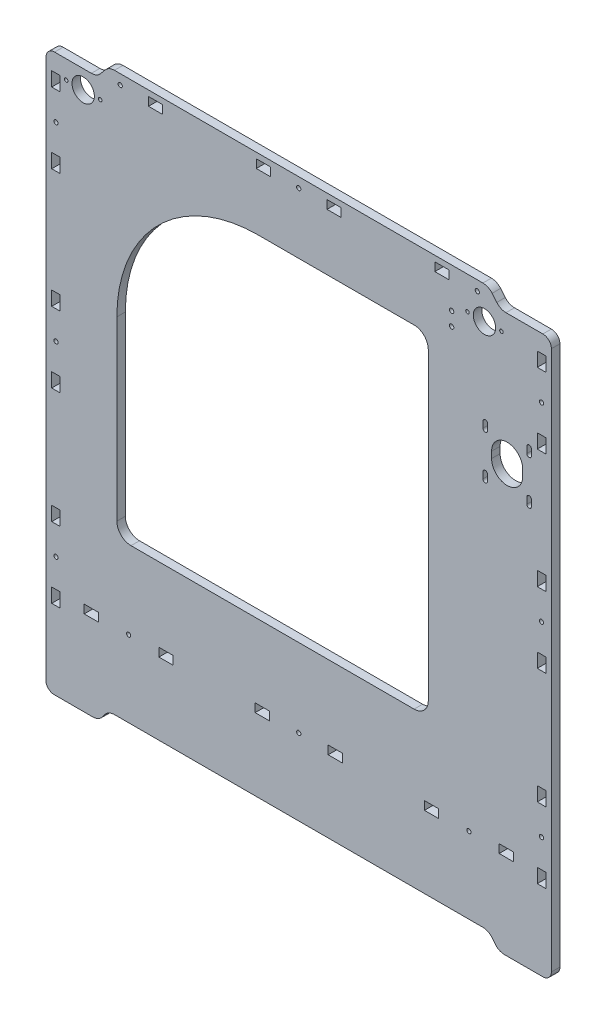
SolidWorks part; units mm, degrees
ref_plane "Спереди" through (0, 0, 0) normal (0, 0, 1) x (1, 0, 0)
ref_plane "Сверху" through (0, 0, 0) normal (0, 1, 0) x (1, 0, 0)
ref_plane "Справа" through (0, 0, 0) normal (1, 0, 0) x (0, 0, -1)
sketch "Эскиз1" plane through (0, 0, 0) normal (0, 0, 1) x (1, 0, 0)
  line L0 (133.6555, 83.4698) -> (133.6555, 87.9698)
  line L1 (133.6555, 118.9698) -> (133.6555, 114.4698)
  line L2 (130.4555, 83.4698) -> (130.4555, 87.9698)
  line L3 (158.5555, 98.9698) -> (158.5555, 103.4698)
  line L4 (130.4555, 118.9698) -> (130.4555, 114.4698)
  line L5 (161.4555, 118.9698) -> (161.4555, 114.4698)
  line L6 (164.6555, 118.9698) -> (164.6555, 114.4698)
  line L7 (136.5555, 98.9698) -> (136.5555, 103.4698)
  line L8 (161.4555, 83.4698) -> (161.4555, 87.9698)
  line L9 (164.6555, 83.4698) -> (164.6555, 87.9698)
  line L10 (-174.1809, 36.7423) -> (-174.1809, 46.7423)
  line L11 (99.1091, -139.9977) -> (89.1091, -139.9977)
  line L12 (89.1091, -139.9977) -> (89.1091, -133.9977)
  line L13 (89.1091, -133.9977) -> (99.1091, -133.9977)
  line L14 (99.1091, -133.9977) -> (99.1091, -139.9977)
  line L15 (151.9091, -139.9977) -> (141.9091, -139.9977)
  line L16 (141.9091, -139.9977) -> (141.9091, -133.9977)
  line L17 (141.9091, -133.9977) -> (151.9091, -133.9977)
  line L18 (151.9091, -133.9977) -> (151.9091, -139.9977)
  line L19 (-19.6709, 193.3023) -> (-29.6709, 193.3023)
  line L20 (-29.6709, 193.3023) -> (-29.6709, 199.3023)
  line L21 (-29.6709, 199.3023) -> (-19.6709, 199.3023)
  line L22 (-19.6709, 199.3023) -> (-19.6709, 193.3023)
  line L23 (30.3091, 193.3023) -> (20.3091, 193.3023)
  line L24 (20.3091, 193.3023) -> (20.3091, 199.3023)
  line L25 (20.3091, 199.3023) -> (30.3091, 199.3023)
  line L26 (30.3091, 199.3023) -> (30.3091, 193.3023)
  line L27 (-141.2709, -139.9977) -> (-151.2709, -139.9977)
  line L28 (-151.2709, -139.9977) -> (-151.2709, -133.9977)
  line L29 (-151.2709, -133.9977) -> (-141.2709, -133.9977)
  line L30 (-141.2709, -133.9977) -> (-141.2709, -139.9977)
  line L31 (-88.4709, -139.9977) -> (-98.4709, -139.9977)
  line L32 (-98.4709, -139.9977) -> (-98.4709, -133.9977)
  line L33 (-98.4709, -133.9977) -> (-88.4709, -133.9977)
  line L34 (-88.4709, -133.9977) -> (-88.4709, -139.9977)
  line L35 (-20.4709, -139.9977) -> (-30.4709, -139.9977)
  line L36 (-30.4709, -139.9977) -> (-30.4709, -133.9977)
  line L37 (-30.4709, -133.9977) -> (-20.4709, -133.9977)
  line L38 (-20.4709, -133.9977) -> (-20.4709, -139.9977)
  line L39 (31.1091, -139.9977) -> (21.1091, -139.9977)
  line L40 (21.1091, -139.9977) -> (21.1091, -133.9977)
  line L41 (21.1091, -133.9977) -> (31.1091, -133.9977)
  line L42 (31.1091, -133.9977) -> (31.1091, -139.9977)
  line L43 (-174.1809, 46.7423) -> (-168.1809, 46.7423)
  line L44 (-168.1809, 46.7423) -> (-168.1809, 36.7423)
  line L45 (-168.1809, 36.7423) -> (-174.1809, 36.7423)
  line L46 (-174.1809, -13.2577) -> (-174.1809, -3.2577)
  line L47 (-174.1809, -3.2577) -> (-168.1809, -3.2577)
  line L48 (-168.1809, -3.2577) -> (-168.1809, -13.2577)
  line L49 (-168.1809, -13.2577) -> (-174.1809, -13.2577)
  line L50 (-174.1809, 170.9023) -> (-174.1809, 180.9023)
  line L51 (-174.1809, 180.9023) -> (-168.1809, 180.9023)
  line L52 (-168.1809, 180.9023) -> (-168.1809, 170.9023)
  line L53 (-168.1809, 170.9023) -> (-174.1809, 170.9023)
  line L54 (-174.1809, 120.9023) -> (-174.1809, 130.9023)
  line L55 (-174.1809, 130.9023) -> (-168.1809, 130.9023)
  line L56 (-168.1809, 130.9023) -> (-168.1809, 120.9023)
  line L57 (-168.1809, 120.9023) -> (-174.1809, 120.9023)
  line L58 (-174.1809, -94.9877) -> (-174.1809, -84.9877)
  line L59 (-174.1809, -84.9877) -> (-168.1809, -84.9877)
  line L62 (-174.1809, -144.9777) -> (-174.1809, -134.9777)
  line L63 (-174.1809, -134.9777) -> (-168.1809, -134.9777)
  line L64 (-168.1809, -134.9777) -> (-168.1809, -144.9777)
  line L65 (-168.1809, -144.9777) -> (-174.1809, -144.9777)
  line L66 (168.8191, 36.7421) -> (168.8191, 46.7421)
  line L67 (168.8191, 46.7421) -> (174.8191, 46.7421)
  line L68 (174.8191, 46.7421) -> (174.8191, 36.7421)
  line L69 (174.8191, 36.7421) -> (168.8191, 36.7421)
  line L70 (168.8191, -13.2579) -> (168.8191, -3.2579)
  line L71 (168.8191, -3.2579) -> (174.8191, -3.2579)
  line L72 (174.8191, -3.2579) -> (174.8191, -13.2579)
  line L73 (174.8191, -13.2579) -> (168.8191, -13.2579)
  line L74 (168.8191, -94.9879) -> (168.8191, -84.9879)
  line L75 (168.8191, -84.9879) -> (174.8191, -84.9879)
  line L76 (174.8191, -84.9879) -> (174.8191, -94.9879)
  line L77 (174.8191, -94.9879) -> (168.8191, -94.9879)
  line L78 (168.8191, -144.9779) -> (168.8191, -134.9779)
  line L79 (168.8191, -134.9779) -> (174.8191, -134.9779)
  line L80 (174.8191, -134.9779) -> (174.8191, -144.9779)
  line L81 (174.8191, -144.9779) -> (168.8191, -144.9779)
  line L82 (168.8191, 170.9021) -> (168.8191, 180.9021)
  line L83 (168.8191, 180.9021) -> (174.8191, 180.9021)
  line L84 (175.1452, 170.9021) -> (168.8191, 170.9021)
  line L85 (168.8191, 120.9021) -> (168.8191, 130.9021)
  line L86 (168.8191, 130.9021) -> (174.8191, 130.9021)
  line L87 (174.8191, 130.9021) -> (174.8191, 120.9021)
  line L88 (174.8191, 120.9021) -> (168.8191, 120.9021)
  line L89 (-105.8209, 199.3023) -> (-95.8209, 199.3023)
  line L90 (-95.8209, 199.3023) -> (-95.8209, 193.3023)
  line L91 (-95.8209, 193.3023) -> (-105.8209, 193.3023)
  line L92 (-105.8209, 193.3023) -> (-105.8209, 199.3023)
  line L94 (96.4591, 193.3023) -> (96.4591, 199.3023)
  line L96 (146.7286, 193.3021) -> (172.7648, 193.3021)
  line L97 (106.4591, 193.3023) -> (96.4591, 193.3023)
  line L99 (-136.3916, 200.266) -> (-139.6874, 196.3386)
  line L100 (130.4099, 203.3023) -> (-129.8802, 203.3023)
  line L101 (136.9212, 200.266) -> (140.2171, 196.3385)
  line L102 (174.8191, 170.9781) -> (175.1452, 170.9021)
  line L104 (96.4591, 199.3023) -> (106.4591, 199.3023)
  line L105 (174.8191, 180.9021) -> (174.8191, 170.9781)
  line L106 (139.2171, -196.9614) -> (136.9212, -193.9418)
  line L107 (-129.8802, -190.9055) -> (130.4099, -190.9055)
  line L108 (-172.2352, -199.9977) -> (-145.1988, -199.9977)
  line L109 (-138.6874, -196.9614) -> (-136.3916, -193.9418)
  line L110 (172.7648, -199.9977) -> (145.7284, -199.9977)
  line L111 (-178.1809, 187.3023) -> (-178.1809, -195.6332)
  line L112 (178.8191, 187.3133) -> (178.8191, -193.998)
  line L113 (-174.1809, -94.9877) -> (-168.1809, -94.9877)
  line L114 (-168.1809, -94.9877) -> (-168.1809, -84.9877)
  line L115 (-172.1809, 193.3023) -> (-146.1988, 193.3023)
  line L116 (106.4591, 199.3023) -> (106.4591, 193.3023)
  line L117 (-198.706, -139.9977) -> (230.9068, -139.9977) construction
  line L118 (-130.8326, 180.3023) -> (-166.8576, 180.3023) construction
  line L119 (113.3107, 180.3023) -> (155.186, 180.3023) construction
  line L121 (-276.4475, 153.3023) -> (140.2171, 153.3023) construction
  line L124 (-128.1809, -71.6977) -> (-128.1809, 53.3023)
  line L126 (-28.1809, 153.3023) -> (81.8191, 153.3023)
  line L127 (91.8191, 143.3023) -> (91.8191, -71.6977)
  line L128 (81.8191, -81.6977) -> (-118.1809, -81.6977)
  arc A0 (158.5555, 103.4698) -> (136.5555, 103.4698) centre (147.5555, 103.4698) ccw
  arc A1 (161.4555, 83.4698) -> (164.6555, 83.4698) centre (163.0555, 83.4698) ccw
  arc A2 (136.5555, 98.9698) -> (158.5555, 98.9698) centre (147.5555, 98.9698) ccw
  arc A3 (130.4555, 83.4698) -> (133.6555, 83.4698) centre (132.0555, 83.4698) ccw
  arc A4 (164.6555, 87.9698) -> (161.4555, 87.9698) centre (163.0555, 87.9698) ccw
  circle A5 centre (108.3191, 165.6023) radius 1.55
  circle A6 centre (108.3191, 175.3023) radius 1.55
  arc A7 (130.4555, 114.4698) -> (133.6555, 114.4698) centre (132.0555, 114.4698) ccw
  arc A8 (133.6555, 118.9698) -> (130.4555, 118.9698) centre (132.0555, 118.9698) ccw
  arc A9 (164.6555, 118.9698) -> (161.4555, 118.9698) centre (163.0555, 118.9698) ccw
  arc A10 (161.4555, 114.4698) -> (164.6555, 114.4698) centre (163.0555, 114.4698) ccw
  arc A11 (133.6555, 87.9698) -> (130.4555, 87.9698) centre (132.0555, 87.9698) ccw
  circle A12 centre (131.5191, 180.3023) radius 7.9
  circle A13 centre (-151.9809, 180.3023) radius 7.9
  arc A14 (-129.8802, 203.3023) -> (-136.3916, 200.266) centre (-129.8802, 194.8023) ccw
  arc A15 (-146.1988, 193.3023) -> (-139.6874, 196.3386) centre (-146.1988, 201.8023) ccw
  arc A17 (140.2171, 196.3385) -> (146.7286, 193.3021) centre (146.7286, 201.8021) ccw
  arc A18 (136.9212, 200.266) -> (130.4099, 203.3023) centre (130.4099, 194.8023) ccw
  arc A19 (178.8191, 187.3133) -> (172.7648, 193.3021) centre (172.8191, 187.3023) ccw
  arc A20 (136.9212, -193.9418) -> (130.4099, -190.9055) centre (130.4099, -199.4055) ccw
  arc A21 (-178.1809, -195.6332) -> (-172.2352, -199.9977) centre (-172.4074, -194.0002) ccw
  arc A22 (-145.1988, -199.9977) -> (-138.6874, -196.9614) centre (-145.1988, -191.4977) ccw
  arc A23 (139.2171, -196.9614) -> (145.7284, -199.9977) centre (145.7284, -191.4977) ccw
  arc A24 (-129.8802, -190.9055) -> (-136.3916, -193.9418) centre (-129.8802, -199.4055) ccw
  circle A25 centre (-171.1809, 150.9023) radius 1.5
  arc A26 (172.7648, -199.9977) -> (178.8191, -193.998) centre (172.8191, -193.998) ccw
  circle A27 centre (-171.1809, 16.7423) radius 1.5
  circle A28 centre (171.8191, 150.9021) radius 1.5
  circle A29 centre (126.4591, 196.3023) radius 1.5
  circle A30 centre (-125.8209, 196.3023) radius 1.5
  circle A31 centre (0.3191, 196.3023) radius 1.5
  circle A32 centre (-119.8709, -136.9977) radius 1.5
  circle A33 centre (-171.1809, -114.9677) radius 1.5
  circle A34 centre (0.3191, -136.9977) radius 1.5
  circle A35 centre (120.5091, -136.9977) radius 1.5
  circle A36 centre (171.8191, -114.9679) radius 1.5
  circle A37 centre (171.8191, 16.7421) radius 1.5
  arc A38 (-178.1809, 187.3023) -> (-172.1809, 193.3023) centre (-172.1809, 187.3023) cw
  circle A39 centre (-139.9809, 180.3023) radius 1.25
  circle A40 centre (-163.9809, 180.3023) radius 1.25
  circle A41 centre (119.5191, 180.3023) radius 1.25
  circle A42 centre (143.5191, 180.3023) radius 1.25
  arc A43 (81.8191, 153.3023) -> (91.8191, 143.3023) centre (81.8191, 143.3023) cw
  arc A44 (91.8191, -71.6977) -> (81.8191, -81.6977) centre (81.8191, -71.6977) cw
  arc A45 (-118.1809, -81.6977) -> (-128.1809, -71.6977) centre (-118.1809, -71.6977) cw
  arc A46 (-128.1809, 53.3023) -> (-28.1809, 153.3023) centre (-28.1809, 53.3023) cw
  point P149 (159.2466, -199.9977)
  point P190 (-105.8209, 196.3023)
  point P191 (171.8191, -13.2579)
  point P192 (174.8191, -89.9879)
  point P193 (-100.8209, 193.3023)
  point P194 (20.3091, 196.3023)
  point P215 (91.8191, 153.3023)
  point P220 (-128.1809, -81.6977)
  point P223 (-128.1809, 153.3023)
  dimension "D9" = 15.8
  dimension "D24" = 8.5
  dimension "D25" = 8.5
  dimension "D26" = 6
  dimension "D27" = 8.5
  dimension "D28" = 8.5
  dimension "D29" = 4
  dimension "D30" = 6
  dimension "D32" = 12.4
  dimension "D40" = 20
  dimension "D82" = 9.7
  dimension "D83" = 28
  dimension "D84" = 70.5
  dimension "D112" = 3
  dimension "D134" = 2.5
  dimension "D135" = 2.5
  dimension "D136" = 12
  dimension "D137" = 12
  dimension "D138" = 2.5
  dimension "D139" = 2.5
  dimension "D140" = 12
  dimension "D141" = 12
  dimension "D146" = 10
  dimension "D147" = 100
  dimension "D3" = 10
  dimension "D4" = 20
  dimension "D5" = 20
  dimension "D6" = 10
  dimension "D7" = 6
  dimension "D8" = 6
  dimension "D10" = 74.16
  dimension "D11" = 10
  dimension "D12" = 6
  dimension "D13" = 20
  dimension "D14" = 6
  dimension "D15" = 10
  dimension "D16" = 71.73
  dimension "D17" = 6
  dimension "D18" = 10
  dimension "D19" = 20.01
  dimension "D20" = 10
  dimension "D21" = 20
  dimension "D22" = 403.3
  dimension "D23" = 19.98
  dimension "D31" = 10
  dimension "D33" = 10
  dimension "D34" = 55.02
  dimension "D35" = 6
  dimension "D36" = 10.0002
  dimension "D37" = 12.4
  dimension "D38" = 10
  dimension "D39" = 20
  dimension "D41" = 6
  dimension "D42" = 6
  dimension "D43" = 74.16
  dimension "D44" = 10
  dimension "D45" = 6
  dimension "D46" = 20
  dimension "D47" = 20
  dimension "D48" = 6
  dimension "D49" = 10
  dimension "D50" = 71.73
  dimension "D51" = 6
  dimension "D52" = 10
  dimension "D53" = 19.98
  dimension "D54" = 10
  dimension "D55" = 6
  dimension "D56" = 20.01
  dimension "D57" = 403.3
  dimension "D58" = 283.5
  dimension "D59" = 55.0198
  dimension "D60" = 357
  dimension "D61" = 26.2
  dimension "D62" = 47.3
  dimension "D63" = 23
  dimension "D64" = 23
  dimension "D65" = 7
  dimension "D66" = 4
  dimension "D67" = 4
  dimension "D68" = 7
  dimension "D69" = 4
  dimension "D70" = 4
  dimension "D71" = 7
  dimension "D72" = 4
  dimension "D73" = 4
  dimension "D74" = 7
  dimension "D75" = 4
  dimension "D76" = 4
  dimension "D77" = 7
  dimension "D78" = 4
  dimension "D79" = 4
  dimension "D80" = 7
  dimension "D81" = 4
  dimension "D85" = 7
  dimension "D86" = 4
  dimension "D87" = 10
  dimension "D88" = 6
  dimension "D89" = 6
  dimension "D90" = 10
  dimension "D91" = 4
  dimension "D92" = 7
  dimension "D93" = 10
  dimension "D94" = 6
  dimension "D95" = 4
  dimension "D96" = 7
  dimension "D97" = 4
  dimension "D98" = 6
  dimension "D99" = 52.36
  dimension "D100" = 20
  dimension "D101" = 66.15
  dimension "D102" = 52.36
  dimension "D103" = 20
  dimension "D104" = 10
  dimension "D105" = 66.15
  dimension "D106" = 178.5
  dimension "D107" = 19.99
  dimension "D108" = 19.99
  dimension "D109" = 60
  dimension "D110" = 10
  dimension "D111" = 6
  dimension "D113" = 10
  dimension "D114" = 6
  dimension "D115" = 10
  dimension "D116" = 6
  dimension "D117" = 3
  dimension "D118" = 6
  dimension "D119" = 10
  dimension "D120" = 10
  dimension "D121" = 6
  dimension "D122" = 3
  dimension "D123" = 6
  dimension "D124" = 10
  dimension "D125" = 178.5
  dimension "D126" = 16.91
  dimension "D127" = 21.4
  dimension "D128" = 21.4
  dimension "D129" = 58
  dimension "D130" = 16.91
  dimension "D131" = 21.4
  dimension "D132" = 21.4
  dimension "D133" = 58
  dimension "D142" = 50
  dimension "D143" = 220
  dimension "D144" = 50
  dimension "D145" = 235
extrude "Бобышка-Вытянуть1" add sketch "Эскиз1" along normal blind 6
